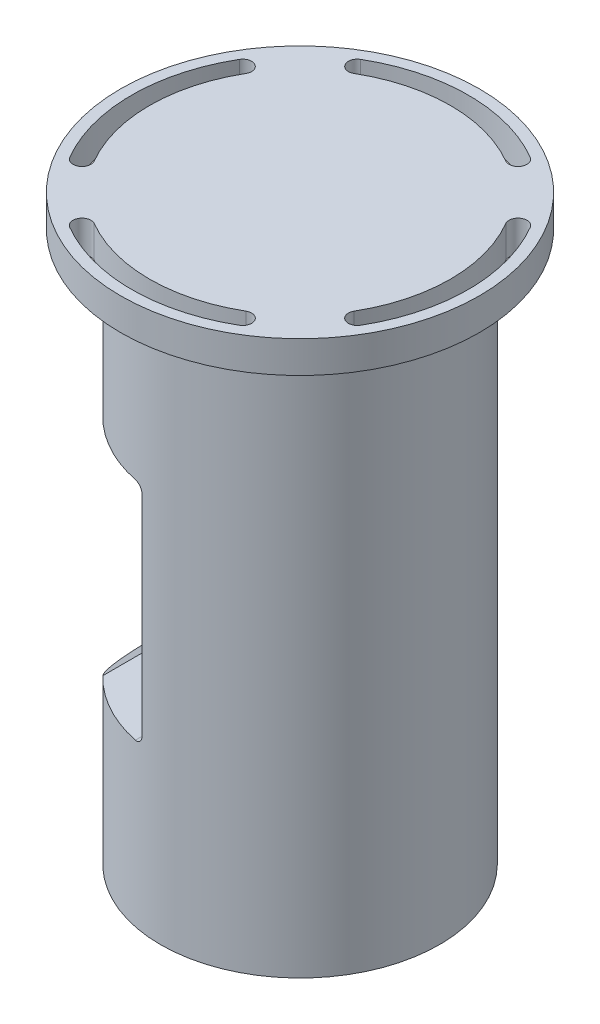
SolidWorks part; units mm, degrees
ref_plane "Alzado" through (0, 0, 0) normal (0, 0, 1) x (1, 0, 0)
ref_plane "Planta" through (0, 0, 0) normal (0, 1, 0) x (1, 0, 0)
ref_plane "Vista lateral" through (0, 0, 0) normal (1, 0, 0) x (0, 0, -1)
sketch "Croquis1" plane through (0, 0, 0) normal (0, 1, 0) x (1, 0, 0)
  circle A0 centre (0, 0) radius 35
  dimension "D1" = 70
extrude "Saliente-Extruir1" add sketch "Croquis1" along normal blind 138
sketch "Croquis2" plane through (0, 138, 0) normal (0, 1, 0) x (1, 0, 0)
  circle A0 centre (0, 0) radius 45
  dimension "D1" = 90
extrude "Saliente-Extruir2" add sketch "Croquis2" along normal blind 8
sketch "Croquis3" plane through (0, 0, 0) normal (0, 0, 1) x (1, 0, 0)
  line L0 (0, 0) -> (0, 154.6028) construction
  line L1 (5, -17.8511) -> (5, 168.7473) construction
  line L2 (5, 0) -> (32.5, 0)
  line L3 (-35, 0) -> (35, 0) construction
  line L4 (32.5, 0) -> (32.5, 22)
  line L5 (32.5, 22) -> (33.5, 22)
  line L6 (33.5, 22) -> (33.5, 25)
  line L7 (33.5, 25) -> (31, 25)
  line L8 (31, 25) -> (31, 113)
  line L9 (31, 113) -> (27.5, 113)
  line L10 (27.5, 113) -> (27.5, 128)
  line L11 (27.5, 128) -> (5, 141)
  line L12 (5, 141) -> (5, 0)
  line L13 (45, 146) -> (-45, 146) construction
  dimension "D1" = 5
  dimension "D2" = 55
  dimension "D3" = 57
  dimension "D4" = 22
  dimension "D5" = 3
  dimension "D6" = 52
  dimension "D7" = 88
  dimension "D8" = 45
  dimension "D9" = 15
  dimension "D10" = 5
revolve "Cortar-Revolución1" cut sketch "Croquis3" angle 360 about L12
sketch "Croquis4" plane through (0, 0, 0) normal (0, 0, 1) x (1, 0, 0)
  line L0 (-35, 32.5) -> (-25.1, 40.6)
  line L1 (-35, 138) -> (-35, 0) construction
  line L2 (-25.1, 40.6) -> (-7, 40.6)
  line L3 (-5, 42.6) -> (-5, 95.2)
  line L4 (-7, 97.2) -> (-25.1, 97.2)
  line L5 (-25.1, 97.2) -> (-35, 105.3)
  line L6 (-35, 105.3) -> (-45, 105.3)
  line L7 (-45, 105.3) -> (-45, 32.5)
  line L8 (-45, 32.5) -> (-35, 32.5)
  line L9 (35, 0) -> (35, 138) construction
  line L10 (-35, 0) -> (35, 0) construction
  line L12 (-45, 138) -> (45, 138) construction
  line L13 (-5, 68.9) -> (-60.2501, 68.9) construction
  arc A0 (-5, 95.2) -> (-7, 97.2) centre (-7, 95.2) ccw
  arc A1 (-7, 40.6) -> (-5, 42.6) centre (-7, 42.6) ccw
  dimension "D10" = 2
  dimension "D1" = 40
  dimension "D2" = 30
  dimension "D3" = 56.6
  dimension "D4" = 40.6
  dimension "D5" = 40.8
  dimension "D6" = 8.1
  dimension "D7" = 9.9
  dimension "D8" = 50.711
  dimension "D9" = 40
extrude "Cortar-Extruir1" cut sketch "Croquis4" against normal mid plane 167
sketch "Croquis5" plane through (0, 138, 0) normal (0, -1, 0) x (1, 0, 0)
  line L0 (0, -54.1771) -> (0, 70.1374) construction
  line L1 (59.2564, 0) -> (-64.1, 0) construction
  line L2 (20.157, -34.5499) -> (0, 0) construction
  line L3 (-20.157, -34.5499) -> (0, 0) construction
  line L4 (-34.5499, -20.157) -> (0, 0) construction
  line L5 (-34.5499, 20.157) -> (0, 0) construction
  line L6 (34.5499, -20.157) -> (0, 0) construction
  line L7 (34.5499, 20.157) -> (0, 0) construction
  line L8 (20.157, 34.5499) -> (0, 0) construction
  line L9 (-20.157, 34.5499) -> (0, 0) construction
  circle A0 centre (0, 0) radius 40 construction
  arc A1 (-20.157, -34.5499) -> (20.157, -34.5499) centre (0, 0) ccw construction
  arc A2 (-21.2908, -36.4933) -> (21.2908, -36.4933) centre (0, 0) ccw
  arc A3 (-19.0232, -32.6065) -> (19.0232, -32.6065) centre (0, 0) ccw
  arc A4 (-19.0232, -32.6065) -> (-21.2908, -36.4933) centre (-20.157, -34.5499) ccw
  arc A5 (21.2908, -36.4933) -> (19.0232, -32.6065) centre (20.157, -34.5499) ccw
  arc A6 (34.5499, -20.157) -> (34.5499, 20.157) centre (0, 0) ccw construction
  arc A7 (36.4933, -21.2908) -> (36.4933, 21.2908) centre (0, 0) ccw
  arc A8 (32.6065, -19.0232) -> (32.6065, 19.0232) centre (0, 0) ccw
  arc A9 (32.6065, -19.0232) -> (36.4933, -21.2908) centre (34.5499, -20.157) ccw
  arc A10 (36.4933, 21.2908) -> (32.6065, 19.0232) centre (34.5499, 20.157) ccw
  arc A11 (-20.157, 34.5499) -> (20.157, 34.5499) centre (0, 0) cw construction
  arc A12 (21.2908, 36.4933) -> (-21.2908, 36.4933) centre (0, 0) ccw
  arc A13 (19.0232, 32.6065) -> (-19.0232, 32.6065) centre (0, 0) ccw
  arc A14 (19.0232, 32.6065) -> (21.2908, 36.4933) centre (20.157, 34.5499) ccw
  arc A15 (-21.2908, 36.4933) -> (-19.0232, 32.6065) centre (-20.157, 34.5499) ccw
  arc A16 (-34.5499, -20.157) -> (-34.5499, 20.157) centre (0, 0) cw construction
  arc A17 (-36.4933, 21.2908) -> (-36.4933, -21.2908) centre (0, 0) ccw
  arc A18 (-32.6065, 19.0232) -> (-32.6065, -19.0232) centre (0, 0) ccw
  arc A19 (-32.6065, 19.0232) -> (-36.4933, 21.2908) centre (-34.5499, 20.157) ccw
  arc A20 (-36.4933, -21.2908) -> (-32.6065, -19.0232) centre (-34.5499, -20.157) ccw
  point P9 (0, -40)
  point P14 (40, 0)
  point P22 (0, 40)
  point P30 (-40, 0)
  dimension "D1" = 80
  dimension "D2" = 4.5
  dimension "D3" = 4.5
  dimension "D4" = 4.5
  dimension "D5" = 4.5
  dimension "D6" = 30.26
  dimension "D7" = 30.26
  dimension "D8" = 30.26
  dimension "D9" = 30.26
  dimension "D10" = 59.74
  dimension "D11" = 30.26
  dimension "D12" = 30.26
  dimension "D13" = 30.26
  dimension "D14" = 30.26
extrude "Cortar-Extruir2" cut sketch "Croquis5" against normal blind 167
hole_wizard "Taladro roscado M41" positions "Croquis8" profile "Croquis7" tap size "M4" standard "DIN"
sketch "Croquis8" plane through (0, 0, 0) normal (0, -1, 0) x (1, 0, 0)
  point P0 (-30, 0)
  dimension "D1" = 30
sketch "Croquis7" plane through (-30, 0, 0) normal (1, 0, 0) x (0, 0, -1)
  line L0 (0, 0) -> (0, 18.9914)
  line L1 (0, 18.9914) -> (1.65, 18)
  line L2 (1.65, 18) -> (1.65, 0)
  line L5 (1.65, 0) -> (0, 0)
  line L10 (0, 18.9914) -> (-1.65, 18) construction
  line L11 (0, -6.35) -> (0, 107.95) construction
  dimension "Diámetro de perforador para roscar" = 3.3
  dimension "Profundidad de perforador para roscar" = 18
  dimension "Ángulo de perforador" = 118
cosmetic thread "Rosca de taladro1" parameters "D1"=8, "D2"=4
